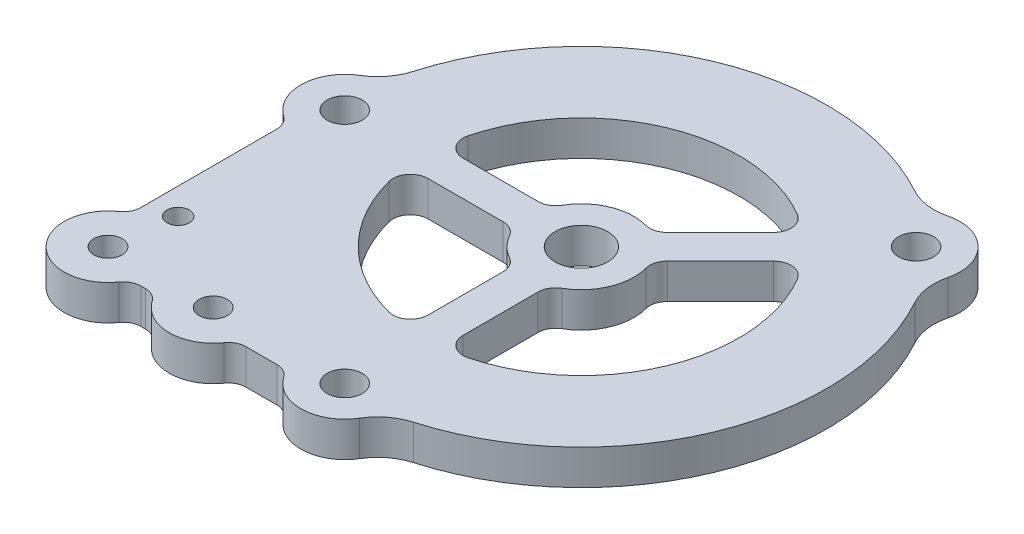
SolidWorks part; units mm, degrees
material "5052-H32"
ref_plane "Front Plane" through (0, 0, 0) normal (0, 0, 1) x (1, 0, 0)
ref_plane "Top Plane" through (0, 0, 0) normal (0, 1, 0) x (1, 0, 0)
ref_plane "Right Plane" through (0, 0, 0) normal (1, 0, 0) x (0, 0, -1)
sketch "Sketch1" plane through (0, 0, 0) normal (0, 1, 0) x (1, 0, 0)
  arc A0 (-42.7069, -12.3258) -> (-12.3258, -42.7069) centre (0, 0) ccw
  circle A1 centre (0, 0) radius 42.8625 construction
  arc A2 (-46.9515, 6.8032) -> (-46.9515, -6.8032) centre (-42.8625, 0) ccw
  arc A3 (-6.8032, -46.9515) -> (6.8032, -46.9515) centre (0, -42.8625) ccw
  arc A4 (38.0103, 28.3891) -> (28.3891, 38.0103) centre (30.3084, 30.3084) ccw
  arc A5 (21.4826, 38.914) -> (-42.7069, 12.3258) centre (0, 0) ccw
  arc A6 (12.3258, -42.7069) -> (38.914, 21.4826) centre (0, 0) ccw
  arc A7 (28.3891, 38.0103) -> (21.4826, 38.914) centre (26.086, 47.2527) cw
  arc A8 (38.0103, 28.3891) -> (38.914, 21.4826) centre (47.2527, 26.086) ccw
  arc A9 (12.3258, -42.7069) -> (6.8032, -46.9515) centre (14.9671, -51.8583) ccw
  arc A10 (-6.8032, -46.9515) -> (-12.3258, -42.7069) centre (-14.9671, -51.8583) ccw
  arc A11 (-42.7069, -12.3258) -> (-46.9515, -6.8032) centre (-51.8583, -14.9671) ccw
  arc A12 (-42.7069, 12.3258) -> (-46.9515, 6.8032) centre (-51.8583, 14.9671) cw
  point P14 (25.3541, 36.5099)
  point P19 (7.8884, -43.7444)
  dimension "D1" = 88.9
  dimension "D2" = 85.725
  dimension "D5" = 15.875
  dimension "D6" = 9.525
  dimension "D3" = 135
  dimension "D4" = 90
extrude "Boss-Extrude1" add sketch "Sketch1" along normal blind 6.35
sketch "Sketch2" plane through (0, 6.35, 0) normal (0, 1, 0) x (1, 0, 0)
  circle A0 centre (0, 0) radius 4.7625
  dimension "D1" = 9.525
extrude "Cut-Extrude1" cut sketch "Sketch2" against normal through all
hole_wizard "1/4 (0.25) Diameter Hole1" positions "Sketch3" profile "Sketch4" hole size "1/4" standard "ANSI Inch" end condition through all
sketch "Sketch3" plane through (0, 6.35, 0) normal (0, 1, 0) x (1, 0, 0)
  point P0 (-42.8625, 0)
  point P3 (30.3084, 30.3084)
  point P6 (0, -42.8625)
sketch "Sketch4" plane through (-42.8625, 6.35, 0) normal (1, 0, 0) x (0, 0, 1)
  line L0 (0, 0) -> (0, 6.35)
  line L1 (0, 6.35) -> (3.175, 6.35)
  line L2 (3.175, 6.35) -> (3.175, 0)
  line L5 (3.175, 0) -> (0, 0)
  line L11 (0, -6.35) -> (0, 107.95) construction
  dimension "Thru Hole Dia." = 6.35
  dimension "Thru Hole Depth" = 6.35
sketch "Sketch5" plane through (0, 6.35, 0) normal (0, 1, 0) x (1, 0, 0)
  line L2 (-28.3981, 3.175) -> (-8.9803, 3.175)
  line L3 (-28.3981, -3.175) -> (-8.9803, -3.175)
  line L4 (22.3255, 17.8354) -> (8.5951, 4.1049)
  line L5 (17.8354, 22.3255) -> (4.1049, 8.5951)
  line L6 (-3.175, -28.3981) -> (-3.175, -8.9803)
  line L7 (3.175, -28.3981) -> (3.175, -8.9803)
  line L8 (0, 0) -> (0, -42.8625) construction
  line L9 (0, 0) -> (30.3084, 30.3084) construction
  arc A3 (-8.9803, -3.175) -> (-3.175, -8.9803) centre (0, 0) ccw
  arc A4 (-28.3981, -3.175) -> (-3.175, -28.3981) centre (0, 0) ccw
  circle A5 centre (0, 0) radius 4.7625 construction
  arc A6 (3.175, -28.3981) -> (22.3255, 17.8354) centre (0, 0) ccw
  arc A7 (3.175, -8.9803) -> (8.5951, 4.1049) centre (0, 0) ccw
  arc A8 (17.8354, 22.3255) -> (-28.3981, 3.175) centre (0, 0) ccw
  arc A9 (4.1049, 8.5951) -> (-8.9803, 3.175) centre (0, 0) ccw
  point P21 (0, 0)
  dimension "D1" = 57.15
  dimension "D2" = 4.7625
  dimension "D3" = 6.35
  dimension "D4" = 6.35
  dimension "D5" = 6.35
extrude "Cut-Extrude2" cut sketch "Sketch5" against normal through all
fillet "Fillet1" radius 3.175 12 edges at (3.175, 3.175, 28.3981) (-3.175, 3.175, 28.3981) (-28.3981, 3.175, 3.175) (-8.9803, 3.175, 3.175) (-3.175, 3.175, 8.9803) (3.175, 3.175, 8.9803) (8.5951, 3.175, -4.1049) (22.3255, 3.175, -17.8354) (17.8354, 3.175, -22.3255) (4.1049, 3.175, -8.5951) (-8.9803, 3.175, -3.175) (-28.3981, 3.175, -3.175)
sketch "Sketch8" plane through (0, 6.35, 0) normal (0, 1, 0) x (1, 0, 0)
  line L0 (-50.8, 0) -> (-50.8, -42.8625)
  line L1 (-42.8625, -50.8) -> (0, -50.8)
  arc A0 (-46.9515, 6.8032) -> (-46.9515, -6.8032) centre (-42.8625, 0) ccw construction
  arc A1 (-6.8032, -46.9515) -> (6.8032, -46.9515) centre (0, -42.8625) ccw construction
  arc A2 (-42.8625, -50.8) -> (-50.8, -42.8625) centre (-42.8625, -42.8625) cw
  arc A3 (-6.8032, -46.9515) -> (-12.3258, -42.7069) centre (-14.9671, -51.8583) ccw construction
  arc A4 (-42.7069, -12.3258) -> (-12.3258, -42.7069) centre (0, 0) ccw construction
  arc A5 (-42.7069, -12.3258) -> (-46.9515, -6.8032) centre (-51.8583, -14.9671) ccw construction
  arc A6 (-6.8032, -46.9515) -> (0, -50.8) centre (0, -42.8625) ccw
  arc A7 (-6.8032, -46.9515) -> (-12.3258, -42.7069) centre (-14.9671, -51.8583) ccw
  arc A8 (-42.7069, -12.3258) -> (-12.3258, -42.7069) centre (0, 0) ccw
  arc A9 (-42.7069, -12.3258) -> (-46.9515, -6.8032) centre (-51.8583, -14.9671) ccw
  arc A10 (-50.8, 0) -> (-46.9515, -6.8032) centre (-42.8625, 0) ccw
  dimension "D1" = 7.9375
extrude "Boss-Extrude2" add sketch "Sketch8" against normal up to surface (6.35 mm away) up to face at (11.5863, 0, 4.7992)
hole_wizard "#10 Clearance Hole1" positions "Sketch10" profile "Sketch11" hole size "#10" standard "ANSI Inch" end condition through all
sketch "Sketch10" plane through (0, 6.35, 0) normal (0, 1, 0) x (1, 0, 0)
  line L0 (-34.925, 0) -> (-31.75, 0)
  line L2 (-33.3375, 0) -> (-33.3375, -42.8625)
  line L4 (-42.8625, -42.8625) -> (-23.8125, -42.8625)
  circle A0 centre (0, 0) radius 31.75
  circle A1 centre (-42.8625, 0) radius 7.9375
  point P0 (-42.8625, -42.8625)
  point P3 (-23.8125, -42.8625)
  point P24 (-33.3375, -42.8625)
  dimension "D1" = 15.875
  dimension "D2" = 63.5
sketch "Sketch11" plane through (-42.8625, 6.35, 42.8625) normal (1, 0, 0) x (0, 0, 1)
  line L0 (0, 0) -> (0, 6.35)
  line L1 (0, 6.35) -> (2.5527, 6.35)
  line L2 (2.5527, 6.35) -> (2.5527, 0)
  line L5 (2.5527, 0) -> (0, 0)
  line L11 (0, -6.35) -> (0, 107.95) construction
  dimension "Thru Hole Dia." = 5.1054
  dimension "Thru Hole Depth" = 6.35
sketch "Sketch15" plane through (0, 6.35, 0) normal (0, 1, 0) x (1, 0, 0)
  line L0 (-46.0375, -7.2748) -> (-46.0375, -35.5877)
  line L1 (-35.5877, -46.0375) -> (-31.0873, -46.0375)
  line L2 (-16.5377, -46.0375) -> (-7.2748, -46.0375)
  line L3 (-50.8, 0) -> (-50.8, -42.8625) construction
  line L4 (-42.8625, -50.8) -> (0, -50.8) construction
  line L5 (-50.8, 0) -> (-50.8, -42.8625)
  line L6 (-42.8625, -50.8) -> (-23.8125, -50.8)
  line L7 (-23.8125, -50.8) -> (0, -50.8)
  line L8 (-39.6875, -7.2748) -> (-39.6875, -35.5877)
  line L9 (-35.5877, -39.6875) -> (-31.0873, -39.6875)
  arc A0 (-50.8, 0) -> (-46.0375, -7.2748) centre (-42.8625, 0) ccw
  arc A1 (-46.0375, -35.5877) -> (-50.8, -42.8625) centre (-42.8625, -42.8625) ccw
  arc A2 (-31.0873, -46.0375) -> (-23.8125, -50.8) centre (-23.8125, -42.8625) ccw
  arc A3 (-7.2748, -46.0375) -> (0, -50.8) centre (0, -42.8625) ccw
  arc A4 (-23.8125, -50.8) -> (-16.5377, -46.0375) centre (-23.8125, -42.8625) ccw
  arc A5 (-42.8625, -50.8) -> (-35.5877, -46.0375) centre (-42.8625, -42.8625) ccw
  arc A6 (-39.6875, -35.5877) -> (-35.5877, -39.6875) centre (-42.8625, -42.8625) cw
  arc A7 (-31.0873, -39.6875) -> (-26.7598, -35.4925) centre (-23.8125, -42.8625) cw
  arc A8 (-39.6875, -7.2748) -> (-43.7444, -7.8884) centre (-42.8625, 0) ccw
  arc A9 (-43.7444, -7.8884) -> (-26.7598, -35.4925) centre (0, 0) ccw
  arc A12 (21.4826, 38.914) -> (-42.7069, 12.3258) centre (0, 0) ccw construction
  point P24 (-33.3375, -46.0375)
  line M13 (-42.8625, -50.8) -> (0, -50.8)
  line M23 (-50.8, 0) -> (-50.8, -42.8625)
  dimension "D1" = 3.175
  dimension "D2" = 3.175
  dimension "D3" = 6.35
  dimension "D4" = 6.35
extrude "Cut-Extrude5" cut sketch "Sketch15" against normal blind 6.35 contours A1 L0 A0 M23 | A5 A2 L1 M13 | A4 A3 L2 M13
fillet "Fillet3" radius 3.175 6 edges at (-7.2748, 3.175, 46.0375) (-16.5377, 3.175, 46.0375) (-46.0375, 3.175, 35.5877) (-46.0375, 3.175, 7.2748) (-31.0873, 3.175, 46.0375) (-35.5877, 3.175, 46.0375)
hole_wizard "#10-32 Tapped Hole1" positions "Sketch16" profile "Sketch17" tap size "#10-32" standard "ANSI Inch" end condition through all
sketch "Sketch16" plane through (0, 6.35, 0) normal (0, 1, 0) x (1, 0, 0)
  line L0 (-46.0375, -9.1195) -> (-46.0375, -33.743) construction
  circle A0 centre (-42.8625, -42.8625) radius 2.5527 construction
  point P0 (-41.275, -31.75)
  dimension "D2" = 4.7625
  dimension "D1" = 11.1125
sketch "Sketch17" plane through (-41.275, 6.35, 31.75) normal (1, 0, 0) x (0, 0, 1)
  line L0 (0, 0) -> (0, 6.35)
  line L1 (0, 6.35) -> (2.0193, 6.35)
  line L2 (2.0193, 6.35) -> (2.0193, 0)
  line L5 (2.0193, 0) -> (0, 0)
  line L11 (0, -6.35) -> (0, 107.95) construction
  dimension "Thread Major Dia." = 4.0386
  dimension "Thru Tap Drill Depth" = 6.35
